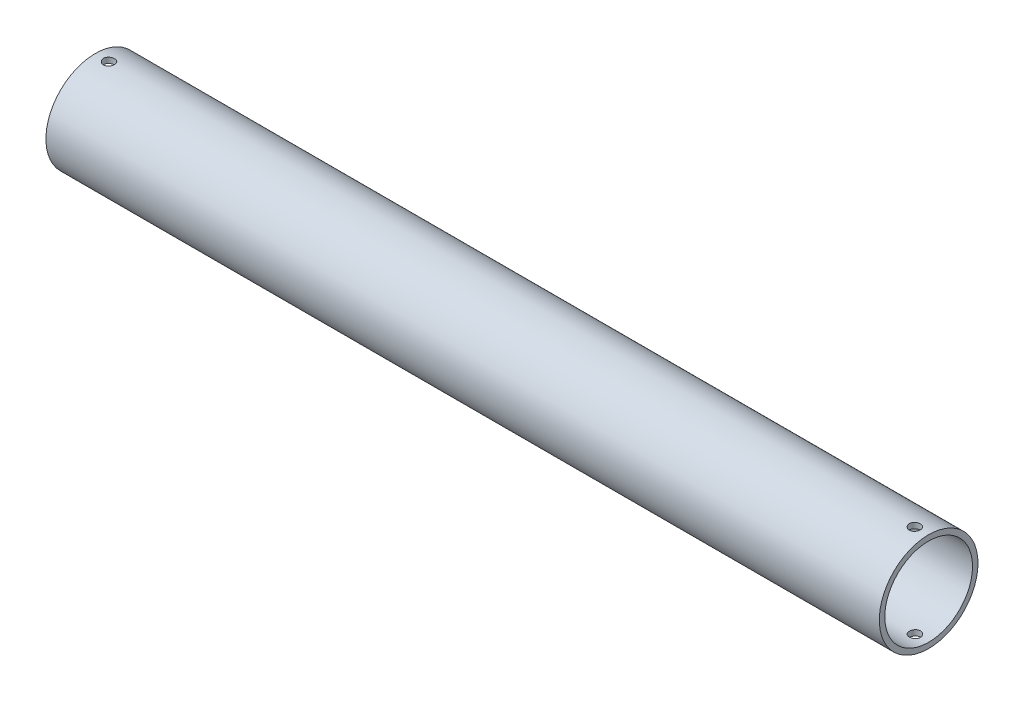
SolidWorks part; units mm, degrees
ref_plane "Front Plane" through (0, 0, 0) normal (0, 0, 1) x (1, 0, 0)
ref_plane "Top Plane" through (0, 0, 0) normal (0, 1, 0) x (1, 0, 0)
ref_plane "Right Plane" through (0, 0, 0) normal (1, 0, 0) x (0, 0, -1)
sketch "Sketch1" plane through (0, 0, 0) normal (1, 0, 0) x (0, 0, -1)
  circle A0 centre (0, 0) radius 28.575
  circle A1 centre (0, 0) radius 25.4
  dimension "D1" = 50.8
  dimension "D2" = 57.15
extrude "Boss-Extrude1" add sketch "Sketch1" along normal blind 482.6
sketch "Sketch2" plane through (0, 0, 0) normal (0, 1, 0) x (1, 0, 0)
  line L0 (241.3, 28.575) -> (241.3, -93.0466) construction
  line L1 (482.6, 28.575) -> (0, 28.575) construction
  line L2 (0, 28.575) -> (0, -28.575) construction
  circle A0 centre (7.9764, 0) radius 3.175
  circle A1 centre (474.6236, 0) radius 3.175
  dimension "D1" = 6.35
  dimension "D2" = 7.9764
extrude "Cut-Extrude1" cut sketch "Sketch2" against normal through all both and the other way through all
ref_plane "Plane1" through (0, 28.575, 0) normal (0, 1, 0) x (1, 0, 0)
